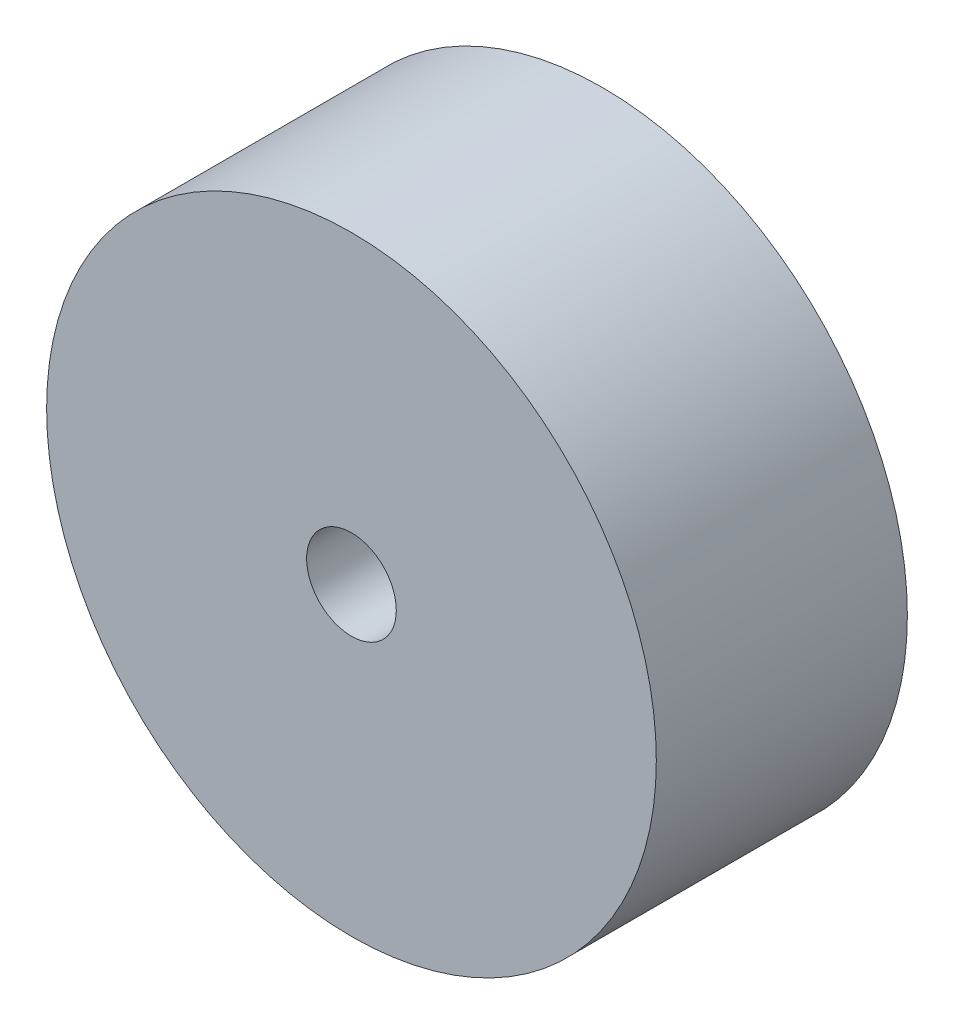
SolidWorks part; units mm, degrees
material "Thornel Mat VMA"
ref_plane "前视基准面" through (0, 0, 0) normal (0, 0, 1) x (1, 0, 0)
ref_plane "上视基准面" through (0, 0, 0) normal (0, 1, 0) x (1, 0, 0)
ref_plane "右视基准面" through (0, 0, 0) normal (1, 0, 0) x (0, 0, -1)
other "Configuration Table"
sketch "草图1" plane through (0, 0, 0) normal (0, 0, 1) x (1, 0, 0)
  circle A0 centre (-6.7835, 17.0584) radius 34
  circle A1 centre (-6.7835, 17.0584) radius 5
  dimension "D1" = 68
  dimension "D2" = 10
extrude "凸台-拉伸1" add sketch "草图1" along normal blind 28
